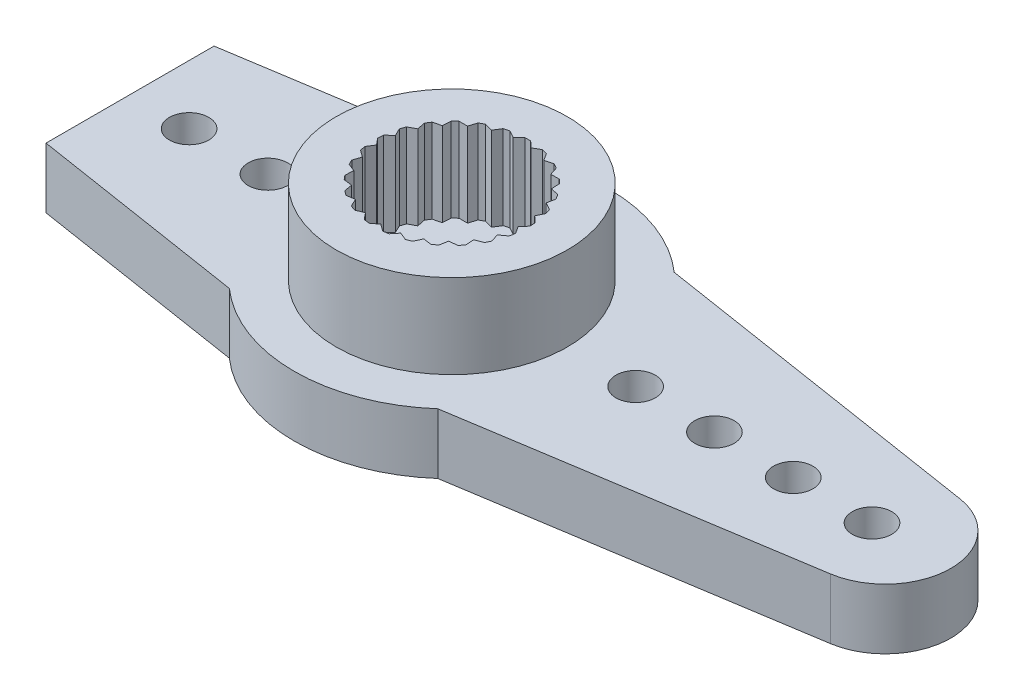
SolidWorks part; units mm, degrees
material "ABS"
ref_plane "Front Plane" through (0, 0, 0) normal (0, 0, 1) x (1, 0, 0)
ref_plane "Top Plane" through (0, 0, 0) normal (0, 1, 0) x (1, 0, 0)
ref_plane "Right Plane" through (0, 0, 0) normal (1, 0, 0) x (0, 0, -1)
sketch "Sketch2" plane through (0, 0, 0) normal (0, 1, 0) x (1, 0, 0)
  circle A0 centre (0, 0) radius 6
  circle A1 centre (0, 0) radius 1.5
  dimension "D1" = 12
  dimension "D2" = 3
extrude "Boss-Extrude1" add sketch "Sketch2" along normal mid plane 2.3
sketch "Sketch3" plane through (0, 1.15, 0) normal (0, 1, 0) x (1, 0, 0)
  line L0 (0, 0) -> (0, 2.9) construction
  line L3 (0, 0) -> (0.376, 2.9763) construction
  line L52 (0.1074, 2.898) -> (0.3384, 2.6787)
  line L53 (-0.1074, 2.898) -> (-0.3384, 2.6787)
  line L54 (0.8248, 2.7802) -> (0.9939, 2.5104)
  line L55 (0.6167, 2.8337) -> (0.3384, 2.6787)
  line L56 (1.4903, 2.4878) -> (1.587, 2.1843)
  line L57 (1.302, 2.5913) -> (0.9939, 2.5104)
  line L58 (2.0621, 2.039) -> (2.0804, 1.721)
  line L59 (1.9055, 2.1861) -> (1.587, 2.1843)
  line L60 (2.5044, 1.4621) -> (2.443, 1.1496)
  line L61 (2.3893, 1.6435) -> (2.0804, 1.721)
  line L62 (2.7894, 0.7934) -> (2.6522, 0.5059)
  line L63 (2.723, 0.9977) -> (2.443, 1.1496)
  line L64 (2.899, 0.0748) -> (2.6947, -0.1695)
  line L65 (2.8855, 0.2892) -> (2.6522, 0.5059)
  line L66 (2.8265, -0.6486) -> (2.5679, -0.8343)
  line L67 (2.8668, -0.4375) -> (2.6947, -0.1695)
  line L68 (2.5765, -1.3311) -> (2.2797, -1.4467)
  line L69 (2.6679, -1.1367) -> (2.5679, -0.8343)
  line L70 (2.1645, -1.93) -> (1.8483, -1.9682)
  line L71 (2.3014, -1.7645) -> (2.2797, -1.4467)
  line L72 (1.6165, -2.4077) -> (1.3007, -2.366)
  line L73 (1.7903, -2.2814) -> (1.8483, -1.9682)
  line L74 (0.967, -2.734) -> (0.6715, -2.6152)
  line L75 (1.1667, -2.655) -> (1.3007, -2.366)
  line L76 (0.2566, -2.8886) -> (0, -2.7)
  line L77 (0.4698, -2.8617) -> (0.6715, -2.6152)
  line L78 (-0.4698, -2.8617) -> (-0.6715, -2.6152)
  line L79 (-0.2566, -2.8886) -> (0, -2.7)
  line L80 (-1.1667, -2.655) -> (-1.3007, -2.366)
  line L81 (-0.967, -2.734) -> (-0.6715, -2.6152)
  line L82 (-1.7903, -2.2814) -> (-1.8483, -1.9682)
  line L83 (-1.6165, -2.4077) -> (-1.3007, -2.366)
  line L84 (-2.3014, -1.7645) -> (-2.2797, -1.4467)
  line L85 (-2.1645, -1.93) -> (-1.8483, -1.9682)
  line L86 (-2.6679, -1.1367) -> (-2.5679, -0.8343)
  line L87 (-2.5765, -1.3311) -> (-2.2797, -1.4467)
  line L88 (-2.8668, -0.4375) -> (-2.6947, -0.1695)
  line L89 (-2.8265, -0.6486) -> (-2.5679, -0.8343)
  line L90 (-2.8855, 0.2892) -> (-2.6522, 0.5059)
  line L91 (-2.899, 0.0748) -> (-2.6947, -0.1695)
  line L92 (-2.723, 0.9977) -> (-2.443, 1.1496)
  line L93 (-2.7894, 0.7934) -> (-2.6522, 0.5059)
  line L94 (-2.3893, 1.6435) -> (-2.0804, 1.721)
  line L95 (-2.5044, 1.4621) -> (-2.443, 1.1496)
  line L96 (-1.9055, 2.1861) -> (-1.587, 2.1843)
  line L97 (-2.0621, 2.039) -> (-2.0804, 1.721)
  line L98 (-1.302, 2.5913) -> (-0.9939, 2.5104)
  line L99 (-1.4903, 2.4878) -> (-1.587, 2.1843)
  line L100 (-0.6167, 2.8337) -> (-0.3384, 2.6787)
  line L101 (-0.8248, 2.7802) -> (-0.9939, 2.5104)
  line L102 (-2.533, 1.6075) -> (-2.3893, 1.6435) construction
  line L103 (-2.533, 1.6075) -> (-2.5044, 1.4621) construction
  line L104 (-2.8532, 0.9271) -> (-2.723, 0.9977) construction
  line L105 (-2.8532, 0.9271) -> (-2.7894, 0.7934) construction
  line L106 (-2.9941, 0.1884) -> (-2.8855, 0.2892) construction
  line L107 (-2.9941, 0.1884) -> (-2.899, 0.0748) construction
  line L108 (-2.9469, -0.5621) -> (-2.8668, -0.4375) construction
  line L109 (-2.9469, -0.5621) -> (-2.8265, -0.6486) construction
  line L110 (0, 3) -> (0.1074, 2.898) construction
  line L111 (0, 2.9) -> (0, 3) construction
  line L112 (0, 3) -> (-0.1074, 2.898) construction
  line L113 (-0.7461, 2.9057) -> (-0.6167, 2.8337) construction
  line L114 (-0.7461, 2.9057) -> (-0.8248, 2.7802) construction
  line L115 (-1.4453, 2.6289) -> (-1.302, 2.5913) construction
  line L116 (-1.4453, 2.6289) -> (-1.4903, 2.4878) construction
  line L117 (-2.0536, 2.1869) -> (-1.9055, 2.1861) construction
  line L118 (-2.0536, 2.1869) -> (-2.0621, 2.039) construction
  line L119 (-2.7145, -1.2773) -> (-2.6679, -1.1367) construction
  line L120 (-2.7145, -1.2773) -> (-2.5765, -1.3311) construction
  line L121 (-2.3115, -1.9123) -> (-2.3014, -1.7645) construction
  line L122 (-2.3115, -1.9123) -> (-2.1645, -1.93) construction
  line L123 (-1.7634, -2.4271) -> (-1.7903, -2.2814) construction
  line L124 (-1.7634, -2.4271) -> (-1.6165, -2.4077) construction
  line L125 (-1.1044, -2.7893) -> (-1.1667, -2.655) construction
  line L126 (-1.1044, -2.7893) -> (-0.967, -2.734) construction
  line L127 (-0.376, -2.9763) -> (-0.4698, -2.8617) construction
  line L128 (-0.376, -2.9763) -> (-0.2566, -2.8886) construction
  line L129 (0.376, -2.9763) -> (0.2566, -2.8886) construction
  line L130 (0.376, -2.9763) -> (0.4698, -2.8617) construction
  line L131 (1.1044, -2.7893) -> (0.967, -2.734) construction
  line L132 (1.1044, -2.7893) -> (1.1667, -2.655) construction
  line L133 (1.7634, -2.4271) -> (1.6165, -2.4077) construction
  line L134 (1.7634, -2.4271) -> (1.7903, -2.2814) construction
  line L135 (2.3115, -1.9123) -> (2.3014, -1.7645) construction
  line L136 (2.3115, -1.9123) -> (2.1645, -1.93) construction
  line L137 (2.7145, -1.2773) -> (2.6679, -1.1367) construction
  line L138 (2.7145, -1.2773) -> (2.5765, -1.3311) construction
  line L139 (2.9469, -0.5621) -> (2.8668, -0.4375) construction
  line L140 (2.9469, -0.5621) -> (2.8265, -0.6486) construction
  line L141 (2.9941, 0.1884) -> (2.8855, 0.2892) construction
  line L142 (2.9941, 0.1884) -> (2.899, 0.0748) construction
  line L143 (2.8532, 0.9271) -> (2.723, 0.9977) construction
  line L144 (2.8532, 0.9271) -> (2.7894, 0.7934) construction
  line L145 (2.533, 1.6075) -> (2.3893, 1.6435) construction
  line L146 (2.533, 1.6075) -> (2.5044, 1.4621) construction
  line L147 (2.0536, 2.1869) -> (1.9055, 2.1861) construction
  line L148 (2.0536, 2.1869) -> (2.0621, 2.039) construction
  line L149 (1.4453, 2.6289) -> (1.302, 2.5913) construction
  line L150 (1.4453, 2.6289) -> (1.4903, 2.4878) construction
  line L151 (0.7461, 2.9057) -> (0.6167, 2.8337) construction
  line L152 (0.7461, 2.9057) -> (0.8248, 2.7802) construction
  circle A0 centre (0, 0) radius 4.4
  circle A1 centre (0, 0) radius 3 construction
  circle A2 centre (0, 0) radius 2.7 construction
  arc A3 (-0.6167, 2.8337) -> (-0.8248, 2.7802) centre (0, 0) ccw
  arc A4 (-0.1074, 2.898) -> (-0.6167, 2.8337) centre (0, 0) ccw construction
  arc A5 (-0.8248, 2.7802) -> (-1.302, 2.5913) centre (0, 0) ccw construction
  arc A6 (-1.302, 2.5913) -> (-1.4903, 2.4878) centre (0, 0) ccw
  arc A7 (-1.4903, 2.4878) -> (-1.9055, 2.1861) centre (0, 0) ccw construction
  arc A8 (-1.9055, 2.1861) -> (-2.0621, 2.039) centre (0, 0) ccw
  arc A9 (-2.0621, 2.039) -> (-2.3893, 1.6435) centre (0, 0) ccw construction
  arc A10 (-2.3893, 1.6435) -> (-2.5044, 1.4621) centre (0, 0) ccw
  arc A11 (-2.5044, 1.4621) -> (-2.723, 0.9977) centre (0, 0) ccw construction
  arc A12 (-2.723, 0.9977) -> (-2.7894, 0.7934) centre (0, 0) ccw
  arc A13 (-2.7894, 0.7934) -> (-2.8855, 0.2892) centre (0, 0) ccw construction
  arc A14 (-2.8855, 0.2892) -> (-2.899, 0.0748) centre (0, 0) ccw
  arc A15 (-2.899, 0.0748) -> (-2.8668, -0.4375) centre (0, 0) ccw construction
  arc A16 (-2.8668, -0.4375) -> (-2.8265, -0.6486) centre (0, 0) ccw
  arc A17 (-2.8265, -0.6486) -> (-2.6679, -1.1367) centre (0, 0) ccw construction
  arc A18 (-2.6679, -1.1367) -> (-2.5765, -1.3311) centre (0, 0) ccw
  arc A19 (-2.5765, -1.3311) -> (-2.3014, -1.7645) centre (0, 0) ccw construction
  arc A20 (-2.3014, -1.7645) -> (-2.1645, -1.93) centre (0, 0) ccw
  arc A21 (-2.1645, -1.93) -> (-1.7903, -2.2814) centre (0, 0) ccw construction
  arc A22 (-1.7903, -2.2814) -> (-1.6165, -2.4077) centre (0, 0) ccw
  arc A23 (-1.6165, -2.4077) -> (-1.1667, -2.655) centre (0, 0) ccw construction
  arc A24 (-1.1667, -2.655) -> (-0.967, -2.734) centre (0, 0) ccw
  arc A25 (-0.967, -2.734) -> (-0.4698, -2.8617) centre (0, 0) ccw construction
  arc A26 (-0.4698, -2.8617) -> (-0.2566, -2.8886) centre (0, 0) ccw
  arc A27 (-0.2566, -2.8886) -> (0.2566, -2.8886) centre (0, 0) ccw construction
  arc A28 (0.2566, -2.8886) -> (0.4698, -2.8617) centre (0, 0) ccw
  arc A29 (0.4698, -2.8617) -> (0.967, -2.734) centre (0, 0) ccw construction
  arc A30 (0.967, -2.734) -> (1.1667, -2.655) centre (0, 0) ccw
  arc A31 (1.1667, -2.655) -> (1.6165, -2.4077) centre (0, 0) ccw construction
  arc A32 (1.6165, -2.4077) -> (1.7903, -2.2814) centre (0, 0) ccw
  arc A33 (1.7903, -2.2814) -> (2.1645, -1.93) centre (0, 0) ccw construction
  arc A34 (2.1645, -1.93) -> (2.3014, -1.7645) centre (0, 0) ccw
  arc A35 (2.3014, -1.7645) -> (2.5765, -1.3311) centre (0, 0) ccw construction
  arc A36 (2.5765, -1.3311) -> (2.6679, -1.1367) centre (0, 0) ccw
  arc A37 (2.6679, -1.1367) -> (2.8265, -0.6486) centre (0, 0) ccw construction
  arc A38 (2.8265, -0.6486) -> (2.8668, -0.4375) centre (0, 0) ccw
  arc A39 (2.8668, -0.4375) -> (2.899, 0.0748) centre (0, 0) ccw construction
  arc A40 (2.899, 0.0748) -> (2.8855, 0.2892) centre (0, 0) ccw
  arc A41 (2.8855, 0.2892) -> (2.7894, 0.7934) centre (0, 0) ccw construction
  arc A42 (2.7894, 0.7934) -> (2.723, 0.9977) centre (0, 0) ccw
  arc A43 (2.723, 0.9977) -> (2.5044, 1.4621) centre (0, 0) ccw construction
  arc A44 (2.5044, 1.4621) -> (2.3893, 1.6435) centre (0, 0) ccw
  arc A45 (2.3893, 1.6435) -> (2.0621, 2.039) centre (0, 0) ccw construction
  arc A46 (2.0621, 2.039) -> (1.9055, 2.1861) centre (0, 0) ccw
  arc A47 (1.9055, 2.1861) -> (1.4903, 2.4878) centre (0, 0) ccw construction
  arc A48 (1.4903, 2.4878) -> (1.302, 2.5913) centre (0, 0) ccw
  arc A49 (1.302, 2.5913) -> (0.8248, 2.7802) centre (0, 0) ccw construction
  arc A50 (0.8248, 2.7802) -> (0.6167, 2.8337) centre (0, 0) ccw
  arc A51 (0.3635, 2.8771) -> (0.1074, 2.898) centre (0, 0) ccw construction
  arc A52 (0.1074, 2.898) -> (-0.1074, 2.898) centre (0, 0) ccw
  arc A53 (0.6167, 2.8337) -> (0.3635, 2.8771) centre (0, 0) ccw construction
  point P84 (0, 0)
  dimension "D1" = 8.8
  dimension "D2" = 5.4
  dimension "D3" = 6
  dimension "D6" = 5.8
  dimension "D4" = 7.2
  dimension "D5" = 25
extrude "Boss-Extrude2" add sketch "Sketch3" along normal blind 3.2
sketch "Sketch4" plane through (0, 0, 0) normal (0, 1, 0) x (1, 0, 0)
  line L0 (0, 0) -> (16, 0) construction
  line L1 (3.9686, 4.5) -> (16.8881, 2.4697)
  line L2 (3.9686, -4.5) -> (16.8881, -2.4697)
  line L3 (16, 0) -> (13, 0) construction
  circle A0 centre (0, 0) radius 6 construction
  arc A1 (3.9686, -4.5) -> (3.9686, 4.5) centre (0, 0) ccw
  arc A2 (16.8881, 2.4697) -> (16.8881, -2.4697) centre (16.5, 0) cw
  circle A3 centre (16, 0) radius 0.75
  circle A4 centre (13, 0) radius 0.75
  circle A5 centre (10, 0) radius 0.75
  circle A6 centre (7, 0) radius 0.75
  dimension "D3" = 2.5
  dimension "D5" = 1.5
  dimension "D2" = 9
  dimension "D7" = 3
  dimension "D4" = 0.5
  dimension "D1" = 16
  dimension "D6" = 4
extrude "Boss-Extrude3" add sketch "Sketch4" along normal mid plane 2.3
pattern_circular "CirPattern1" count 2 over 360 about axis through (0, 0, 0) along (0, 1, 0) of "Boss-Extrude3"
sketch "Sketch5" [suppressed] plane through (0, 0, 0) normal (0, 1, 0) x (1, 0, 0)
  line L0 (3, 7) -> (-3, 7) construction
  circle A0 centre (0, 0) radius 10
  circle A1 centre (0, 7) radius 0.75
  circle A2 centre (-3, 7) radius 0.75
  circle A3 centre (3, 7) radius 0.75
  circle A4 centre (7, 3) radius 0.75
  circle A5 centre (7, 0) radius 0.75
  circle A6 centre (7, -3) radius 0.75
  circle A7 centre (3, -7) radius 0.75
  circle A8 centre (0, -7) radius 0.75
  circle A9 centre (-3, -7) radius 0.75
  circle A10 centre (-7, -3) radius 0.75
  circle A11 centre (-7, 0) radius 0.75
  circle A12 centre (-7, 3) radius 0.75
  circle A13 centre (0, 0) radius 1.5 construction
  circle A14 centre (0, 0) radius 1.5
  point P8 (0, 7)
  point P31 (0, 0)
  dimension "D1" = 1.5
  dimension "D3" = 2.25
  dimension "D4" = 6
  dimension "D2" = 7
  dimension "D5" = 4
extrude "Boss-Extrude4" [suppressed] add sketch "Sketch5" along normal mid plane 2.3
sketch "Sketch6" plane through (0, -1.15, 0) normal (0, -1, 0) x (1, 0, 0)
  line L2 (-12.25, 0) -> (-12.25, 5.9327)
  line L3 (-12.25, 5.9327) -> (-21.2932, 5.9327)
  line L4 (-21.2932, 0) -> (-21.2932, 5.9327)
  line L6 (-21.2932, 0) -> (-21.2932, -7.3716)
  line L7 (-21.2932, -7.3716) -> (-12.25, -7.3716)
  line L8 (-12.25, 0) -> (-12.25, -7.3716)
  circle A0 centre (-13, 0) radius 0.75 construction
extrude "Cut-Extrude1" cut sketch "Sketch6" against normal blind 10
equation "\"N_hole\"= 4"
equation "\"N_horn\"= 2"
equation "\"D6@Sketch4\"=\"N_hole\""
equation "\"D1@CirPattern1\"=\"N_horn\""
equation "\"D1@Sketch4\"=(\"N_hole\" - 1) *3 +7"
